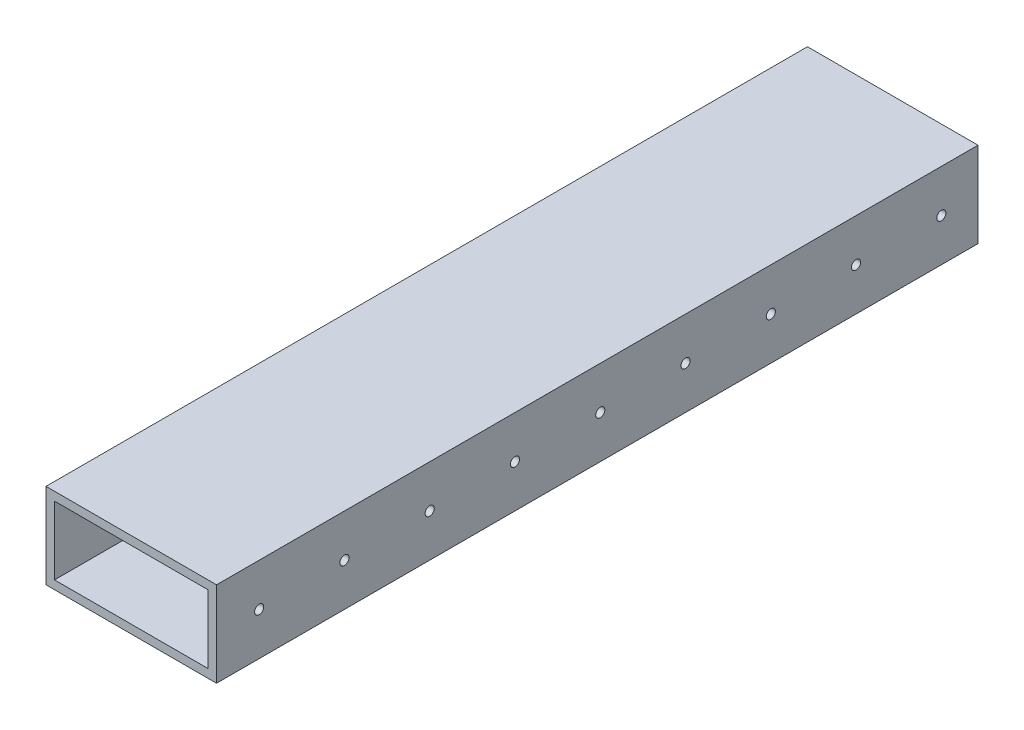
SolidWorks part; units mm, degrees
ref_plane "Front" through (0, 0, 0) normal (0, 0, 1) x (1, 0, 0)
ref_plane "Top" through (0, 0, 0) normal (0, 1, 0) x (1, 0, 0)
ref_plane "Right" through (0, 0, 0) normal (1, 0, 0) x (0, 0, -1)
sketch "Sketch1" plane through (0, 0, 0) normal (0, 0, 1) x (1, 0, 0)
  line L1 (-25.4, -12.7) -> (25.4, -12.7)
  line L2 (-25.4, -12.7) -> (-25.4, 12.7)
  line L3 (-25.4, 12.7) -> (25.4, 12.7)
  line L4 (25.4, -12.7) -> (25.4, 12.7)
  line L5 (-25.4, -12.7) -> (25.4, 12.7) construction
  line L6 (-25.4, 12.7) -> (25.4, -12.7) construction
  point P0 (0, 0)
  dimension "D1" = 25.4
  dimension "D2" = 50.8
extrude "Extrude-Thin1" add sketch "Sketch1" along normal mid plane 226.822 thin thin type one direction reverse wall 2.54
sketch "Sketch2" plane through (25.4, 0, 0) normal (1, 0, 0) x (0, 0, -1)
  line L0 (-113.411, 0) -> (113.411, 0) construction
  line L1 (-113.411, -12.7) -> (-113.411, 12.7) construction
  line L2 (113.411, -12.7) -> (113.411, 12.7) construction
  circle A0 centre (-100.711, 0) radius 1.3589
  dimension "D1" = 12.7
  dimension "D2" = 2.7178
extrude "Cut-Extrude1" cut sketch "Sketch2" against normal through all
pattern_linear "LPattern1" count 9 spacing 25.4 along (0, 0, -1) of "Cut-Extrude1"
